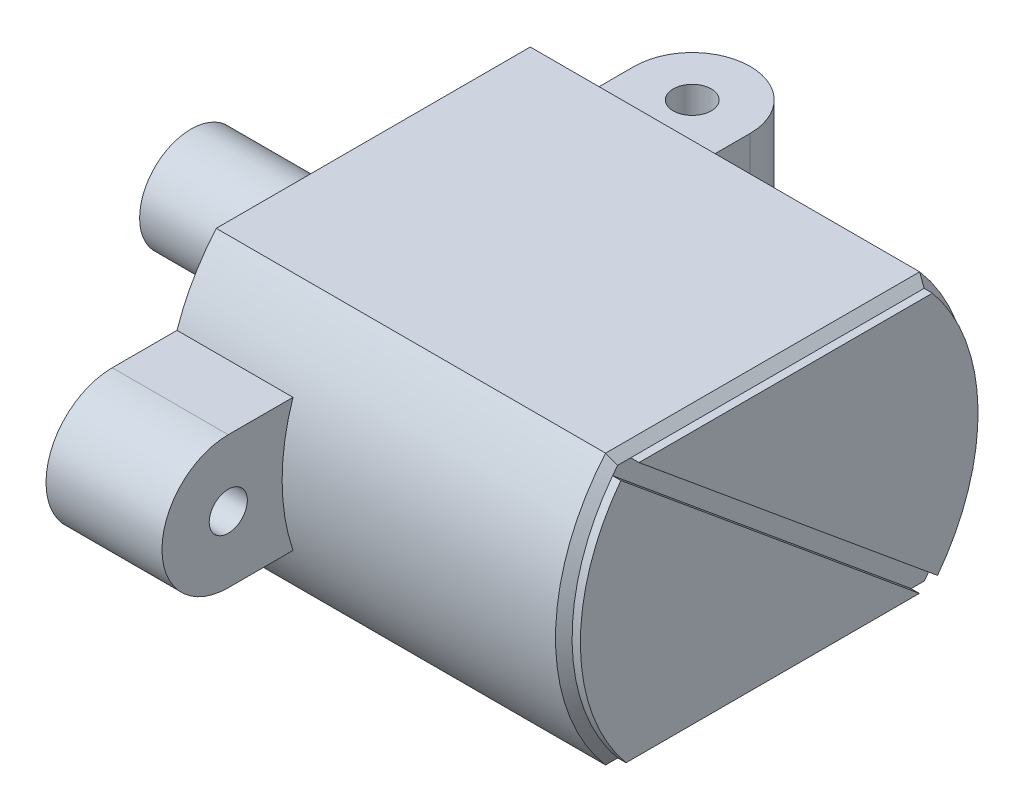
SolidWorks part; units mm, degrees
ref_plane "前视基准面" through (0, 0, 0) normal (0, 0, 1) x (1, 0, 0)
ref_plane "上视基准面" through (0, 0, 0) normal (0, 1, 0) x (1, 0, 0)
ref_plane "右视基准面" through (0, 0, 0) normal (1, 0, 0) x (0, 0, -1)
sketch "草图1" plane through (0, 0, 0) normal (1, 0, 0) x (0, 0, -1)
  line L1 (9.4777, -8.15) -> (-9.4777, -8.15)
  line L2 (9.4777, -8.15) -> (9.4777, 8.15) construction
  line L3 (9.4777, 8.15) -> (-9.4777, 8.15)
  line L4 (-9.4777, -8.15) -> (-9.4777, 8.15) construction
  line L5 (9.4777, -8.15) -> (-9.4777, 8.15) construction
  line L6 (9.4777, 8.15) -> (-9.4777, -8.15) construction
  arc A0 (-9.4777, 8.15) -> (-9.4777, -8.15) centre (0, 0) ccw
  arc A1 (9.4777, 8.15) -> (-9.4777, 8.15) centre (0, 0) ccw construction
  arc A2 (9.4777, -8.15) -> (9.4777, 8.15) centre (0, 0) ccw
  arc A3 (-9.4777, -8.15) -> (9.4777, -8.15) centre (0, 0) ccw construction
  dimension "D2" = 25
  dimension "D1" = 16.3
extrude "凸台-拉伸1" add sketch "草图1" along normal blind 24
sketch "草图2" plane through (0, 0, 0) normal (-1, 0, 0) x (0, 0, 1)
  line L0 (0, 0) -> (15.75, 0) construction
  line L1 (0, 4) -> (15.75, 4)
  line L2 (0, -4) -> (15.75, -4)
  arc A0 (0, 4) -> (0, -4) centre (0, 0) ccw
  arc A1 (15.75, -4) -> (15.75, 4) centre (15.75, 0) ccw
  circle A2 centre (15.75, 0) radius 1.15
  point P3 (7.875, 0)
  dimension "D2" = 15.75
  dimension "D3" = 2.3
  dimension "D1" = 8
extrude "凸台-拉伸2" add sketch "草图2" against normal blind 7
sketch "草图3" plane through (0, 0, 0) normal (0, 1, 0) x (1, 0, 0)
  line L0 (3.5, 0) -> (3.5, 15.75) construction
  line L1 (0, 0) -> (0, 15.75)
  line L2 (7, 0) -> (7, 15.75)
  line L3 (0, -9.4777) -> (0, 9.4777) construction
  line L4 (3.5, 0) -> (0, 0) construction
  arc A0 (0, 0) -> (7, 0) centre (3.5, 0) ccw
  arc A1 (7, 15.75) -> (0, 15.75) centre (3.5, 15.75) ccw
  circle A2 centre (3.5, 15.75) radius 1.15
  point P2 (3.5, 7.875)
  dimension "D3" = 3.5
  dimension "D4" = 2.3
  dimension "D1" = 3.5
  dimension "D2" = 15.75
extrude "凸台-拉伸3" add sketch "草图3" along normal mid plane 8
sketch "草图4" plane through (0, 0, 0) normal (-1, 0, 0) x (0, 0, 1)
  circle A0 centre (0, 0) radius 3.1
  dimension "D1" = 6.2
extrude "凸台-拉伸4" add sketch "草图4" along normal blind 11
chamfer "倒角4" distance 0.5 angle 45 4 edges at (24, 8.15, 0) (24, 0, -12.5) (24, -8.15, 0) (24, 0, 12.5)
sketch "草图5" plane through (24, 0, 0) normal (1, 0, 0) x (0, 0, -1)
  line L0 (-9.2454, 7.65) -> (9.2454, -7.65) construction
  line L1 (-9.5561, 7.2581) -> (8.4611, -7.65)
  line L2 (9.2454, 7.65) -> (-9.2454, 7.65)
  line L3 (-9.2454, -7.65) -> (9.2454, -7.65)
  line L4 (9.2454, 7.65) -> (-8.4611, 7.65)
  line L5 (-9.2454, -7.65) -> (8.4611, -7.65)
  line L6 (-8.4611, 7.65) -> (9.5561, -7.2581)
  line L7 (-8.4611, 7.65) -> (-9.2454, 7.65) construction
  line L8 (8.4611, -7.65) -> (9.2454, -7.65) construction
  arc A0 (-9.2454, 7.65) -> (-9.5561, 7.2581) centre (0, 0) ccw construction
  arc A1 (9.2454, -7.65) -> (9.5561, -7.2581) centre (0, 0) ccw construction
  arc A2 (9.2454, -7.65) -> (9.2454, 7.65) centre (0, 0) ccw
  arc A3 (-9.2454, 7.65) -> (-9.2454, -7.65) centre (0, 0) ccw
  arc A4 (9.5561, -7.2581) -> (9.2454, 7.65) centre (0, 0) ccw
  arc A5 (-9.5561, 7.2581) -> (-9.2454, -7.65) centre (0, 0) ccw
  dimension "D2" = 0.5
  dimension "D3" = 0.5
  dimension "D1" = 0
extrude "凸台-拉伸5" add sketch "草图5" along normal blind 0.5
